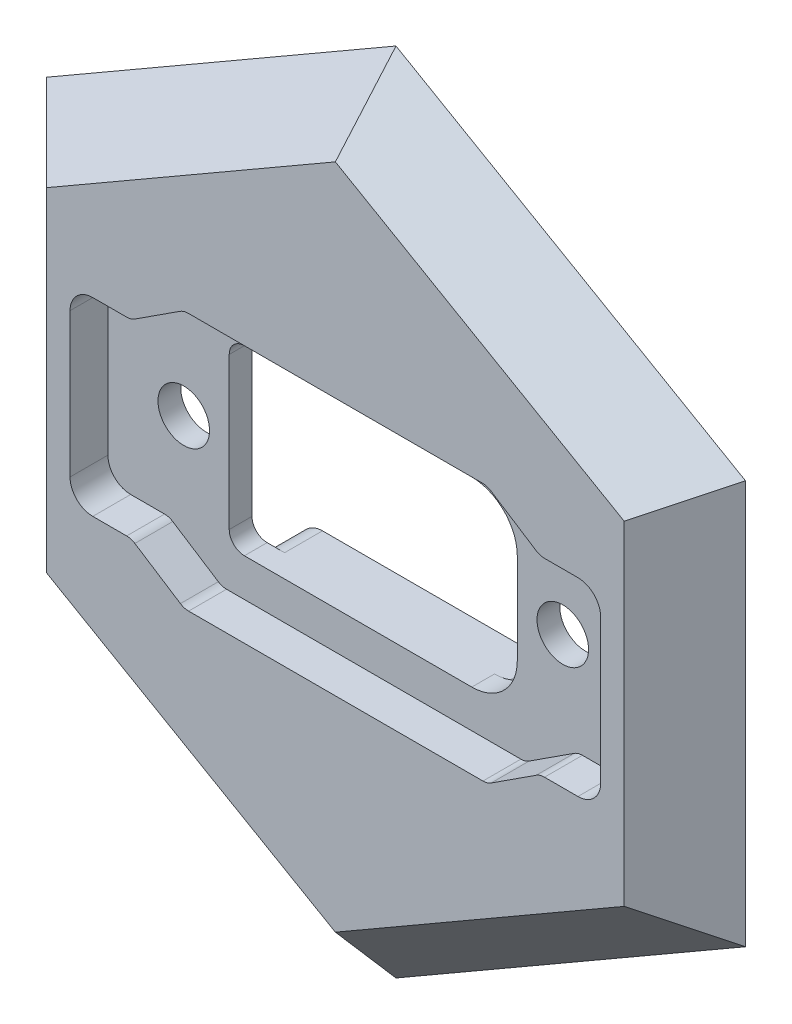
SolidWorks part; units mm, degrees
ref_plane "Płaszczyzna przednia" through (0, 0, 0) normal (0, 0, 1) x (1, 0, 0)
ref_plane "Płaszczyzna górna" through (0, 0, 0) normal (0, 1, 0) x (1, 0, 0)
ref_plane "Płaszczyzna prawa" through (0, 0, 0) normal (1, 0, 0) x (0, 0, -1)
sketch "Sketch1" plane through (0, 0, 0) normal (0, 0, 1) x (1, 0, 0)
  circle A0 centre (0, 0) radius 28
extrude "Boss-Extrude1" add sketch "Sketch1" along normal blind 4
sketch "Sketch2" plane through (0, 0, 0) normal (0, 0, -1) x (-1, 0, 0)
  line L0 (0, 0) -> (0, 6) construction
  line L6 (-7.3485, -6) -> (7.3485, -6)
  line L7 (-10.3923, -6) -> (10.3923, -6) construction
  line L9 (-10.3923, -6) -> (-10.3923, 6) construction
  line L10 (-10.3923, 6) -> (10.3923, 6) construction
  line L11 (10.3923, -6) -> (10.3923, 6) construction
  line L12 (-10.3923, -6) -> (10.3923, 6) construction
  line L13 (-10.3923, 6) -> (10.3923, -6) construction
  line L14 (7.3485, 6) -> (-7.3485, 6)
  arc A6 (-8.3983, -8.5714) -> (8.3983, -8.5714) centre (0, 0) ccw
  arc A7 (8.3983, 8.5714) -> (-8.3983, 8.5714) centre (0, 0) ccw
  arc A8 (-8.3983, -8.5714) -> (-7.3485, -6) centre (-7.3485, -7.5) cw
  arc A9 (8.3983, -8.5714) -> (7.3485, -6) centre (7.3485, -7.5) ccw
  arc A10 (8.3983, 8.5714) -> (7.3485, 6) centre (7.3485, 7.5) cw
  arc A11 (-7.3485, 6) -> (-8.3983, 8.5714) centre (-7.3485, 7.5) cw
  dimension "D1" = 1.5
extrude "Boss-Extrude2" add sketch "Sketch2" along normal blind 2.5
sketch "Sketch3" plane through (0, 0, 4) normal (0, 0, 1) x (1, 0, 0)
  line L0 (0, 8.5) -> (-10, 8.5) construction
  line L1 (-17.5, -6.25) -> (17.5, -6.25) construction
  line L2 (-17.5, -6.25) -> (-17.5, 6.25) construction
  line L3 (-17.5, 6.25) -> (17.5, 6.25) construction
  line L4 (17.5, -6.25) -> (17.5, 6.25) construction
  line L5 (-17.5, -6.25) -> (17.5, 6.25) construction
  line L6 (-17.5, 6.25) -> (17.5, -6.25) construction
  line L7 (-13.5, -8.5) -> (13.5, -8.5) construction
  line L8 (-13.5, -8.5) -> (-13.5, 8.5) construction
  line L9 (-13.5, 8.5) -> (13.5, 8.5) construction
  line L10 (13.5, -8.5) -> (13.5, 8.5) construction
  line L11 (-13.5, -8.5) -> (13.5, 8.5) construction
  line L12 (-13.5, 8.5) -> (13.5, -8.5) construction
  line L13 (0, 8.5) -> (10, 8.5) construction
  line L14 (0, -8.5) -> (-9.9719, -8.5) construction
  line L15 (-9.9719, -8.5) -> (10.0303, -8.5) construction
  line L16 (-17.5, 4.75) -> (-17.5, -4.75)
  line L17 (-16, -6.25) -> (-13.7656, -6.25)
  line L18 (-13.2248, -6.4088) -> (-10.2189, -8.3412)
  line L19 (-9.6782, -8.5) -> (9.7344, -8.5)
  line L20 (10.2785, -8.339) -> (13.2518, -6.411)
  line L21 (13.7959, -6.25) -> (16, -6.25)
  line L22 (17.5, -4.75) -> (17.5, 4.75)
  line L23 (16, 6.25) -> (13.7937, 6.25)
  line L24 (13.2529, 6.4088) -> (10.2471, 8.3412)
  line L25 (9.7063, 8.5) -> (-9.7041, 8.5)
  line L26 (-10.2482, 8.339) -> (-13.2215, 6.411)
  line L27 (-13.7656, 6.25) -> (-16, 6.25)
  arc A0 (17.5, 4.75) -> (16, 6.25) centre (16, 4.75) ccw
  arc A1 (16, -6.25) -> (17.5, -4.75) centre (16, -4.75) ccw
  arc A2 (-17.5, -4.75) -> (-16, -6.25) centre (-16, -4.75) ccw
  arc A3 (-17.5, 4.75) -> (-16, 6.25) centre (-16, 4.75) cw
  arc A4 (-13.2215, 6.411) -> (-13.7656, 6.25) centre (-13.7656, 7.25) cw
  arc A5 (-10.2482, 8.339) -> (-9.7041, 8.5) centre (-9.7041, 7.5) cw
  arc A6 (9.7063, 8.5) -> (10.2471, 8.3412) centre (9.7063, 7.5) cw
  arc A7 (13.7937, 6.25) -> (13.2529, 6.4088) centre (13.7937, 7.25) cw
  arc A8 (13.2518, -6.411) -> (13.7959, -6.25) centre (13.7959, -7.25) cw
  arc A9 (10.2785, -8.339) -> (9.7344, -8.5) centre (9.7344, -7.5) cw
  arc A10 (-10.2189, -8.3412) -> (-9.6782, -8.5) centre (-9.6782, -7.5) ccw
  arc A11 (-13.7656, -6.25) -> (-13.2248, -6.4088) centre (-13.7656, -7.25) cw
  point P0 (0, 0)
  point P6 (0, 0)
  point P35 (-13.4697, 6.25)
  point P44 (13.5, 6.25)
  point P47 (13.5, -6.25)
  point P56 (-13.4719, -6.25)
  dimension "D7" = 1.5
  dimension "D8" = 1
  dimension "D1" = 35
  dimension "D2" = 12.5
  dimension "D3" = 27
  dimension "D4" = 17
  dimension "D5" = 10
  dimension "D6" = 10
extrude "Cut-Extrude1" cut sketch "Sketch3" against normal blind 2.5
sketch "Sketch4" plane through (0, 0, -2.5) normal (0, 0, -1) x (-1, 0, 0)
  line L1 (-6.5, -6) -> (8.5, -6)
  line L2 (-9.5, -3) -> (-9.5, 3)
  line L3 (-6.5, 6) -> (8.5, 6)
  line L4 (9.5, -5) -> (9.5, 5)
  line L5 (-9.5, -6) -> (9.5, 6) construction
  line L6 (-9.5, 6) -> (9.5, -6) construction
  arc A0 (-6.5, -6) -> (-9.5, -3) centre (-6.5, -3) cw
  arc A1 (-9.5, 3) -> (-6.5, 6) centre (-6.5, 3) cw
  arc A2 (8.5, -6) -> (9.5, -5) centre (8.5, -5) ccw
  arc A3 (8.5, 6) -> (9.5, 5) centre (8.5, 5) cw
  point P0 (0, 0)
  dimension "D3" = 3
  dimension "D4" = 1
  dimension "D1" = 19
  dimension "D2" = 12
extrude "Cut-Extrude2" cut sketch "Sketch4" against normal through all
sketch "Sketch5" plane through (0, 0, 1.5) normal (0, 0, 1) x (1, 0, 0)
  line L0 (0, 0) -> (12.5, 0) construction
  line L1 (0, 0) -> (-12.5, 0) construction
  circle A0 centre (-12.5, 0) radius 1.7
  circle A1 centre (12.5, 0) radius 1.7
extrude "Cut-Extrude3" cut sketch "Sketch5" against normal through all
sketch "Sketch7" plane through (0, 0, 4) normal (0, 0, 1) x (1, 0, 0)
  line L1 (0, 22) -> (-19.0526, 11)
  line L2 (-19.0526, 11) -> (-19.0526, -11)
  line L3 (-19.0526, -11) -> (0, -22)
  line L4 (0, -22) -> (19.0526, -11)
  line L5 (19.0526, -11) -> (19.0526, 11)
  line L6 (19.0526, 11) -> (0, 22)
  circle A0 centre (0, 0) radius 22 construction
extrude "Cut-Extrude4" cut sketch "Sketch7" against normal through all draft 45 flip side to cut
